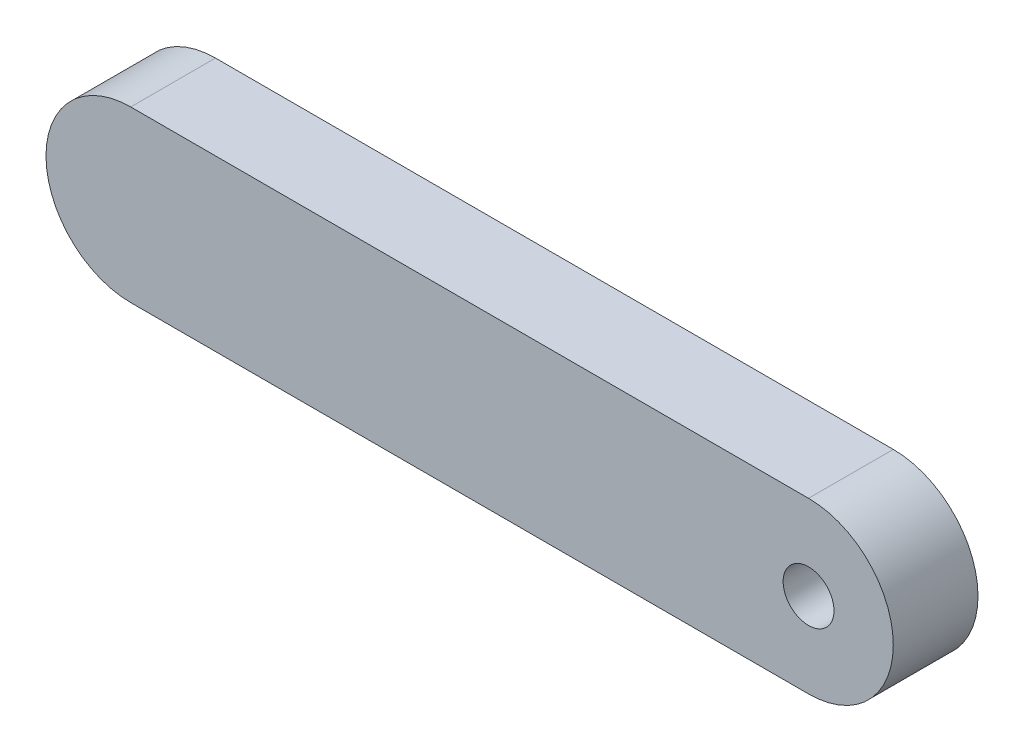
SolidWorks part; units mm, degrees
ref_plane "Front Plane" through (0, 0, 0) normal (0, 0, 1) x (1, 0, 0)
ref_plane "Top Plane" through (0, 0, 0) normal (0, 1, 0) x (1, 0, 0)
ref_plane "Right Plane" through (0, 0, 0) normal (1, 0, 0) x (0, 0, -1)
sketch "Sketch1" plane through (0, 0, 0) normal (0, 0, 1) x (1, 0, 0)
  line L0 (-20, 0) -> (20, 0) construction
  line L1 (-20, 5) -> (20, 5)
  line L2 (-20, -5) -> (20, -5)
  arc A0 (-20, 5) -> (-20, -5) centre (-20, 0) ccw
  arc A1 (20, -5) -> (20, 5) centre (20, 0) ccw
  circle A2 centre (20, 0) radius 1.5
  point P2 (0, 0)
  dimension "D1" = 3
  dimension "D3" = 5
  dimension "D2" = 40
extrude "Boss-Extrude1" add sketch "Sketch1" along normal blind 5
